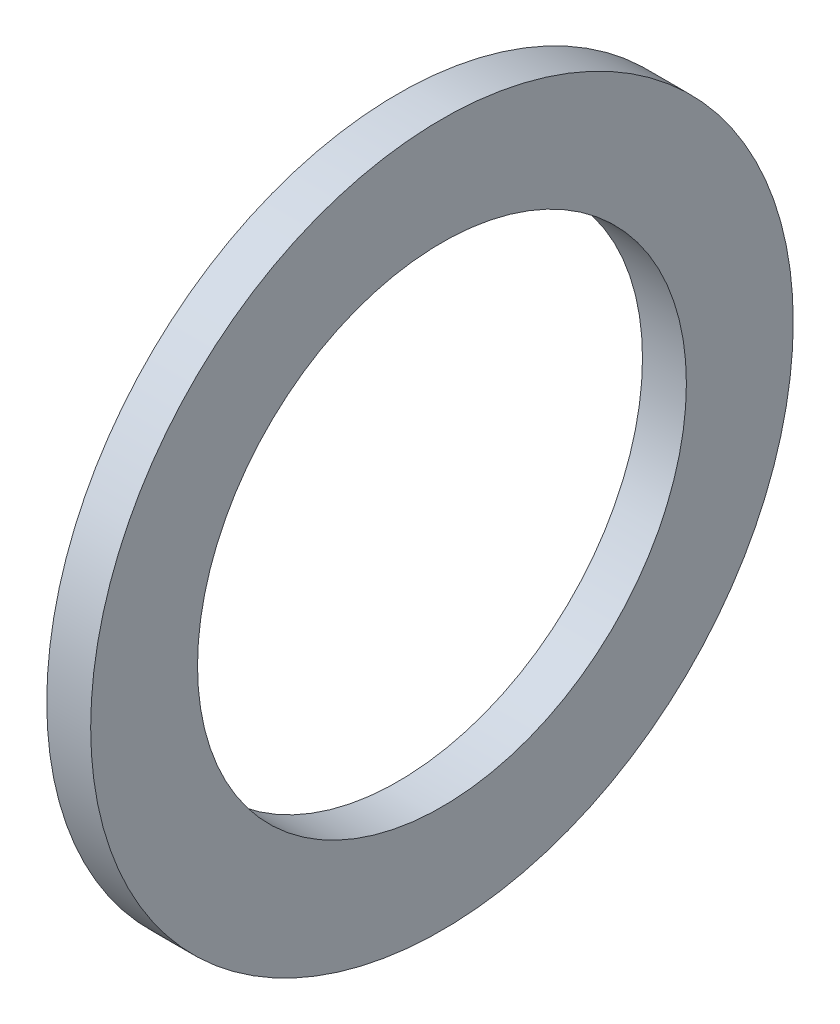
SolidWorks part; units mm, degrees
ref_plane "Front" through (0, 0, 0) normal (0, 0, 1) x (1, 0, 0)
ref_plane "Top" through (0, 0, 0) normal (0, 1, 0) x (1, 0, 0)
ref_plane "Right" through (0, 0, 0) normal (1, 0, 0) x (0, 0, -1)
curve "ImportedCurve1"
curve "ImportedCurve2"
curve "ImportedCurve3"
curve "ImportedCurve4"
curve "ImportedCurve5"
curve "ImportedCurve6"
curve "ImportedCurve7"
curve "ImportedCurve8"
curve "ImportedCurve9"
curve "ImportedCurve10"
curve "ImportedCurve11"
curve "ImportedCurve12"
curve "ImportedCurve13"
curve "ImportedCurve14"
curve "ImportedCurve15"
curve "ImportedCurve16"
curve "ImportedCurve17"
curve "ImportedCurve18"
sketch "Sketch1" plane through (0, 0, 0) normal (0, 0, 1) x (1, 0, 0)
  line L0 (593.1404, 453.5943) -> (590.3124, 453.5943) construction
  line L1 (593.1404, 452.5943) -> (593.1404, 454.5943) construction
  line L2 (591.6404, 465.5943) -> (593.1404, 465.5943)
  line L3 (591.6404, 465.5943) -> (591.6404, 463.1609)
  line L4 (593.1404, 465.5943) -> (593.1404, 463.1609)
  line L5 (591.6404, 463.1609) -> (593.1404, 463.1609)
revolve "Revolve1" add sketch "Sketch1" angle 360 about L0
sketch "Sketch2" plane through (0, 0, 0) normal (0, 0, 1) x (1, 0, 0)
  line L0 (593.1404, 453.5943) -> (591.2554, 453.5943) construction
  line L1 (593.1404, 452.5943) -> (593.1404, 454.5943) construction
  line L3 (593.1404, 461.9443) -> (591.6404, 461.9443)
  line L4 (593.1404, 461.9443) -> (593.1404, 463.1609)
  line L5 (593.1404, 463.1609) -> (591.6404, 463.1609)
  line L6 (591.6404, 461.9443) -> (591.6404, 463.1609)
revolve "Revolve2" add sketch "Sketch2" angle 360 about L0
